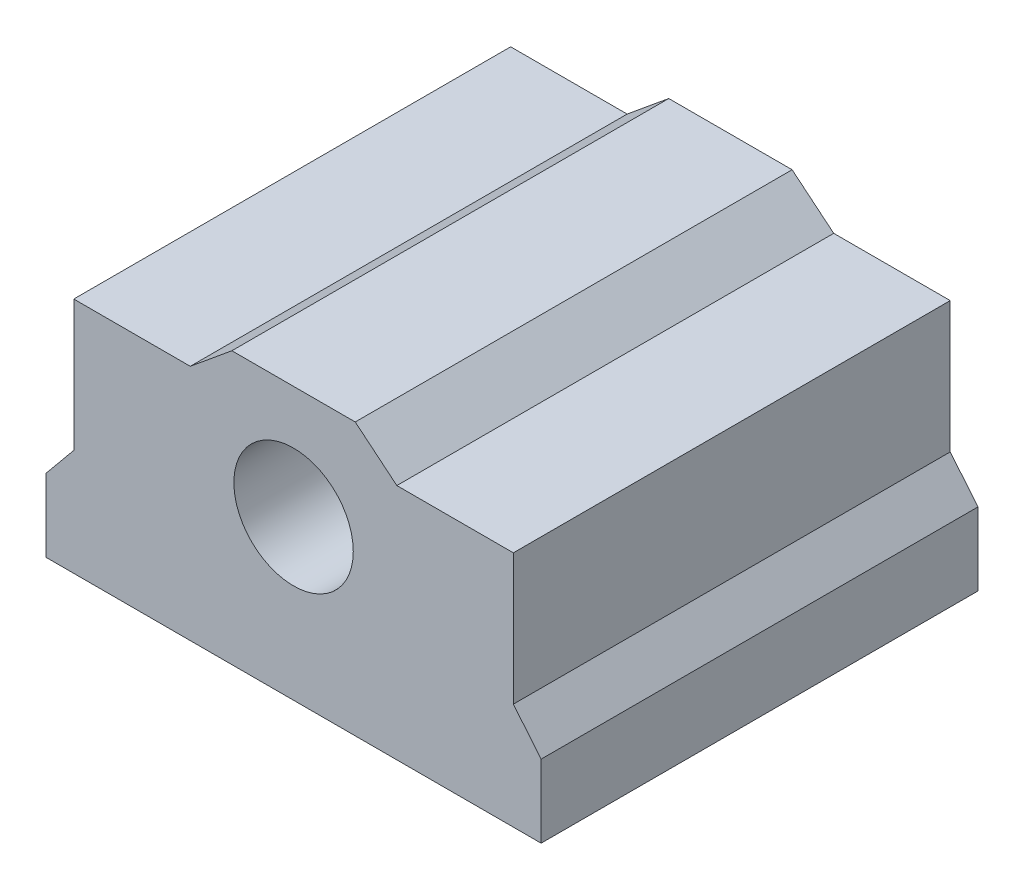
SolidWorks part; units mm, degrees
ref_plane "Front Plane" through (0, 0, 0) normal (0, 0, 1) x (1, 0, 0)
ref_plane "Top Plane" through (0, 0, 0) normal (0, 1, 0) x (1, 0, 0)
ref_plane "Right Plane" through (0, 0, 0) normal (1, 0, 0) x (0, 0, -1)
sketch "Sketch1" plane through (0, 0, 0) normal (0, 0, 1) x (1, 0, 0)
  line L0 (-17, 0) -> (17, 0)
  line L1 (-17, 0) -> (-17, 5)
  line L2 (-17, 5) -> (-15.0927, 7.3157)
  line L3 (-15.0927, 7.3157) -> (-15.0927, 16.3157)
  line L4 (-15.0927, 16.3157) -> (-7.0927, 16.3157)
  line L5 (-7.0927, 16.3157) -> (-4.2359, 18.6687)
  line L6 (-4.2359, 18.6687) -> (4.2359, 18.6687)
  line L7 (4.2359, 18.6687) -> (7.0927, 16.3157)
  line L8 (7.0927, 16.3157) -> (15.0927, 16.3157)
  line L9 (15.0927, 16.3157) -> (15.0927, 7.3157)
  line L10 (15.0927, 7.3157) -> (17, 5)
  line L11 (17, 5) -> (17, 0)
  circle A0 centre (0, 10.9) radius 4.1
  point P3 (0, 0)
  point P9 (-8.2547, 0)
  point P15 (-9.6089, 3.4684)
  point P16 (-6.6155, 11.8426)
  point P17 (-1.7692, 13.5888)
  point P18 (0, 18.6687)
  point P19 (-10.6423, 0)
  point P22 (-9.7158, 3.0051)
  point P23 (-8.5755, 4.5374)
  point P24 (-5.0476, 12.8761)
  point P25 (-5.0476, 14.1946)
  point P26 (7.286, 17.1658)
  point P27 (-15.2693, 7.4505)
  point P28 (-4.2359, 18.6687)
  dimension "D1" = 8.2
  dimension "D2" = 10.9
  dimension "D3" = 34
  dimension "D4" = 5
  dimension "D5" = 3
  dimension "D6" = 9
  dimension "D7" = 8
extrude "Boss-Extrude1" add sketch "Sketch1" along normal blind 30
